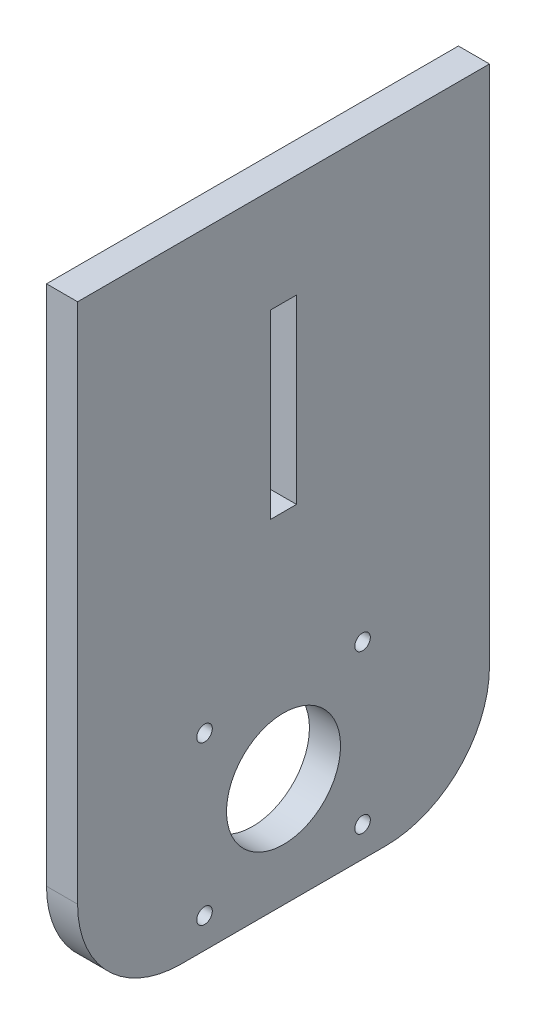
SolidWorks part; units mm, degrees
ref_plane "Front Plane" through (0, 0, 0) normal (0, 0, 1) x (1, 0, 0)
ref_plane "Top Plane" through (0, 0, 0) normal (0, 1, 0) x (1, 0, 0)
ref_plane "Right Plane" through (0, 0, 0) normal (1, 0, 0) x (0, 0, -1)
sketch "Sketch1" plane through (0, 0, 0) normal (1, 0, 0) x (0, 0, -1)
  line L0 (0, 43) -> (0, 120.7)
  line L1 (0, 0) -> (79.5, 0)
  line L2 (0, 0) -> (0, 43)
  line L3 (0, 120.7) -> (79.5, 120.7)
  line L4 (79.5, 0) -> (79.5, 43)
  line L21 (79.5, 43) -> (79.5, 120.7)
  dimension "D1" = 79.5
  dimension "D2" = 120.7
extrude "Boss-Extrude2" add sketch "Sketch1" along normal blind 6 contours L0 L3 L21 L4 L1 L2
sketch "Sketch2" plane through (6, 0, 0) normal (1, 0, 0) x (0, 0, -1)
  line L0 (0, 120.7) -> (79.5, 120.7) construction
  line L1 (37.25, 100.7) -> (42.25, 100.7)
  line L2 (37.25, 100.7) -> (37.25, 65.7)
  line L4 (42.25, 100.7) -> (42.25, 65.7)
  line L6 (37.25, 65.7) -> (42.25, 65.7)
  line L7 (0, 0) -> (79.5, 0) construction
  point P6 (39.75, 120.7)
  point P7 (39.75, 100.7)
  dimension "D1" = 35
  dimension "D2" = 65.7
  dimension "D3" = 5
extrude "Cut-Extrude1" cut sketch "Sketch2" against normal blind 10
sketch "Sketch3" plane through (6, 0, 0) normal (1, 0, 0) x (0, 0, -1)
  line L0 (0, 0) -> (79.5, 0) construction
  line L2 (24.5, 5.85) -> (55, 5.85) construction
  line L3 (24.5, 5.85) -> (24.5, 36.35) construction
  line L4 (24.5, 36.35) -> (55, 36.35) construction
  line L5 (55, 5.85) -> (55, 36.35) construction
  line L6 (24.5, 5.85) -> (55, 36.35) construction
  line L7 (24.5, 36.35) -> (55, 5.85) construction
  circle A0 centre (39.75, 21.1) radius 11
  circle A1 centre (24.5, 36.35) radius 1.5
  circle A2 centre (55, 36.35) radius 1.5
  circle A3 centre (55, 5.85) radius 1.5
  circle A4 centre (24.5, 5.85) radius 1.5
  point P4 (39.75, 0)
  dimension "D1" = 22
  dimension "D4" = 3
  dimension "D2" = 21.1
  dimension "D3" = 30.5
extrude "Cut-Extrude2" cut sketch "Sketch3" against normal blind 10
fillet "Fillet1" radius 20 2 edges at (3, 0, 0) (3, 0, -79.5)
